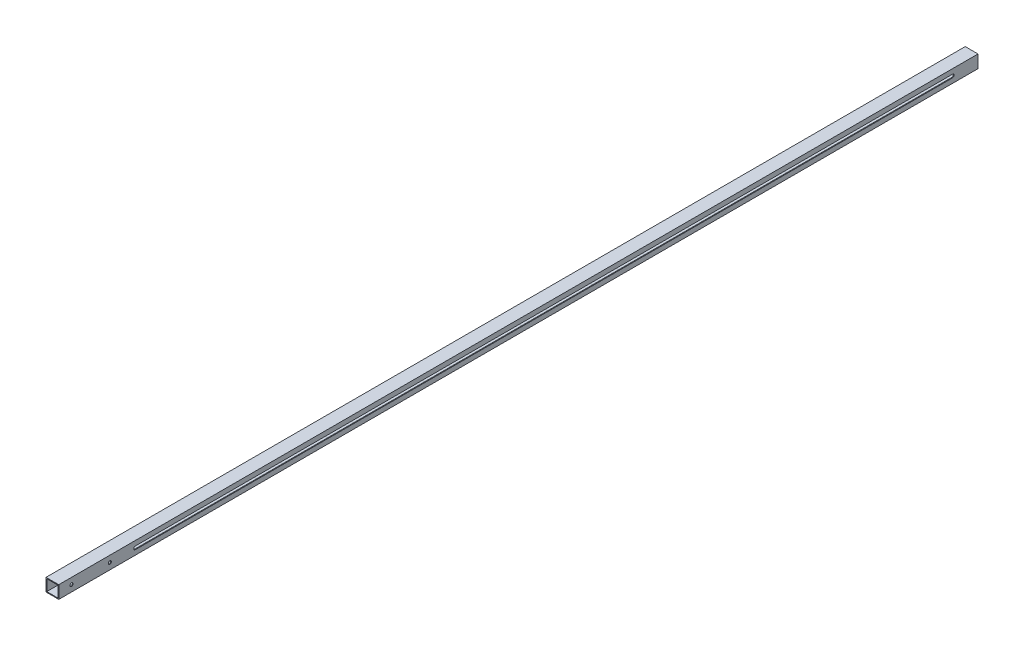
SolidWorks part; units mm, degrees
material "6063-O"
ref_plane "Front Plane" through (0, 0, 0) normal (0, 0, 1) x (1, 0, 0)
ref_plane "Top Plane" through (0, 0, 0) normal (0, 1, 0) x (1, 0, 0)
ref_plane "Right Plane" through (0, 0, 0) normal (1, 0, 0) x (0, 0, -1)
sketch "Sketch1" plane through (0, 0, 0) normal (0, 0, 1) x (1, 0, 0)
  line L1 (-12.7, 12.7) -> (12.7, 12.7)
  line L2 (-12.7, 12.7) -> (-12.7, -12.7)
  line L3 (-12.7, -12.7) -> (12.7, -12.7)
  line L4 (12.7, 12.7) -> (12.7, -12.7)
  line L5 (-12.7, 12.7) -> (12.7, -12.7) construction
  line L6 (-12.7, -12.7) -> (12.7, 12.7) construction
  line L7 (-11.1125, 11.1125) -> (11.1125, 11.1125)
  line L8 (-11.1125, 11.1125) -> (-11.1125, -11.1125)
  line L9 (-11.1125, -11.1125) -> (11.1125, -11.1125)
  line L10 (11.1125, 11.1125) -> (11.1125, -11.1125)
  line L11 (-11.1125, 11.1125) -> (11.1125, -11.1125) construction
  line L12 (-11.1125, -11.1125) -> (11.1125, 11.1125) construction
  point P0 (0, 0)
  point P6 (0, 0)
  dimension "D1" = 25.4
  dimension "D2" = 25.4
  dimension "D3" = 1.5875
extrude "Boss-Extrude1" add sketch "Sketch1" along normal blind 1828.8
sketch "Sketch2" plane through (12.7, 0, 0) normal (1, 0, 0) x (0, 0, -1)
  line L0 (-1828.8, 0) -> (-1727.2, 0) construction
  line L2 (-1828.8, -12.7) -> (-1828.8, 12.7) construction
  circle A0 centre (-1727.2, 0) radius 3.175
  circle A1 centre (-1803.4, 0) radius 3.175
  dimension "D3" = 6.35
  dimension "D4" = 76.2
  dimension "D2" = 6.35
  dimension "D1" = 101.6
extrude "Cut-Extrude1" cut sketch "Sketch2" against normal through all
sketch "Sketch3" plane through (12.7, 0, 0) normal (1, 0, 0) x (0, 0, -1)
  line L0 (-1828.8, 0) -> (0, 0) construction
  line L1 (-1828.8, -12.7) -> (-1828.8, 12.7) construction
  line L2 (0, -12.7) -> (0, 12.7) construction
  line L3 (-1676.4, 0) -> (-50.8, 0) construction
  line L4 (-1676.4, 3.175) -> (-50.8, 3.175)
  line L5 (-1676.4, -3.175) -> (-50.8, -3.175)
  arc A0 (-1676.4, 3.175) -> (-1676.4, -3.175) centre (-1676.4, 0) ccw
  arc A1 (-50.8, -3.175) -> (-50.8, 3.175) centre (-50.8, 0) ccw
  point P8 (-863.6, 0)
  dimension "D1" = 1625.6
  dimension "D2" = 50.8
  dimension "D3" = 6.35
extrude "Cut-Extrude2" cut sketch "Sketch3" against normal through all
